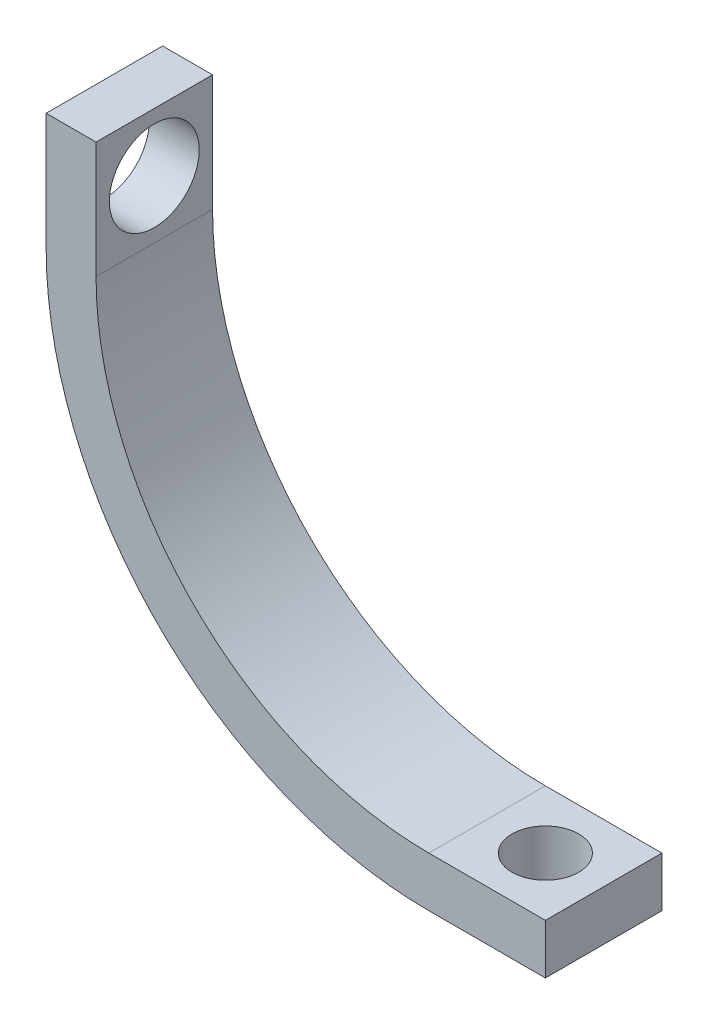
SolidWorks part; units mm, degrees
ref_plane "Front Plane" through (0, 0, 0) normal (0, 0, 1) x (1, 0, 0)
ref_plane "Top Plane" through (0, 0, 0) normal (0, 1, 0) x (1, 0, 0)
ref_plane "Right Plane" through (0, 0, 0) normal (1, 0, 0) x (0, 0, -1)
sketch "Sketch1" plane through (0, 0, 0) normal (0, 0, 1) x (1, 0, 0)
  line L0 (-20, 0) -> (-20, 7)
  line L1 (0, -20) -> (7, -20)
  line L2 (0, -23) -> (7, -23)
  line L3 (-23, 0) -> (-23, 7)
  line L4 (7, -20) -> (7, -23)
  line L5 (-20, 7) -> (-23, 7)
  arc A0 (-20, 0) -> (0, -20) centre (0, 0) ccw
  arc A1 (-23, 0) -> (0, -23) centre (0, 0) ccw
  dimension "D1" = 3
extrude "Boss-Extrude1" add sketch "Sketch1" along normal blind 7
sketch "Sketch2" plane through (-20, 0, 0) normal (1, 0, 0) x (0, 0, -1)
  line L0 (-7, 3.5) -> (0, 3.5) construction
  line L1 (-7, 0) -> (-7, 7) construction
  line L2 (0, 0) -> (0, 7) construction
  line L3 (-3.5, 2.75) -> (-3.5, 4.25) construction
  circle A0 centre (-3.5, 3.5) radius 2.7
  point P11 (-3.5, 3.5)
  point P14 (-3.5, 4.25)
  point P17 (-3.5, 2.75)
extrude "Cut-Extrude1" cut sketch "Sketch2" against normal through all
sketch "Sketch4" plane through (0, -20, 0) normal (0, 1, 0) x (1, 0, 0)
  circle A0 centre (3.5, -3.5) radius 2
extrude "Cut-Extrude2" cut sketch "Sketch4" against normal blind 10
